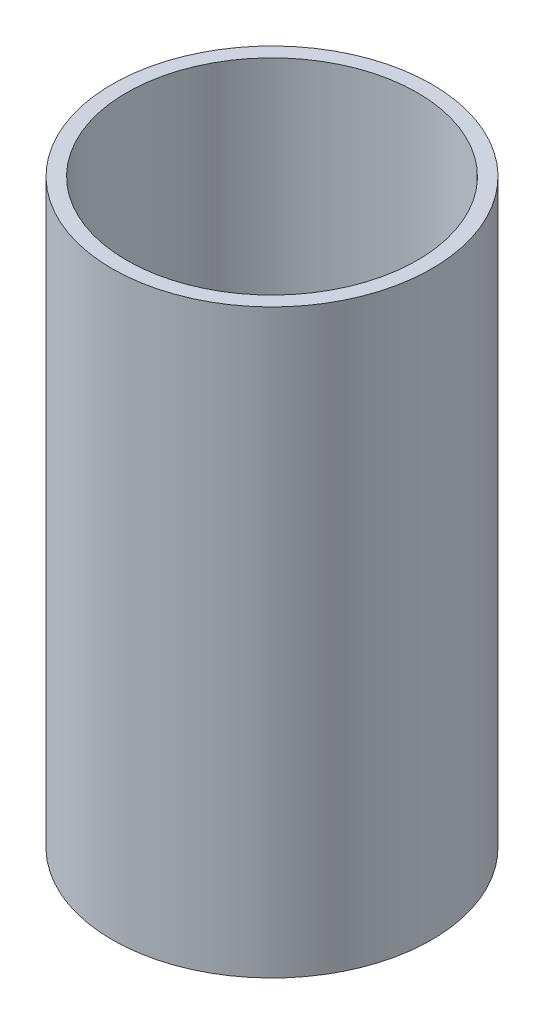
SolidWorks part; units mm, degrees
ref_plane "Front Plane" through (0, 0, 0) normal (0, 0, 1) x (1, 0, 0)
ref_plane "Top Plane" through (0, 0, 0) normal (0, 1, 0) x (1, 0, 0)
ref_plane "Right Plane" through (0, 0, 0) normal (1, 0, 0) x (0, 0, -1)
sketch "Sketch1" plane through (0, 0, 0) normal (0, 1, 0) x (1, 0, 0)
  circle A0 centre (0, 0) radius 30
  circle A1 centre (0, 0) radius 33
  dimension "D1" = 3
extrude "Boss-Extrude1" add sketch "Sketch1" along normal blind 120
